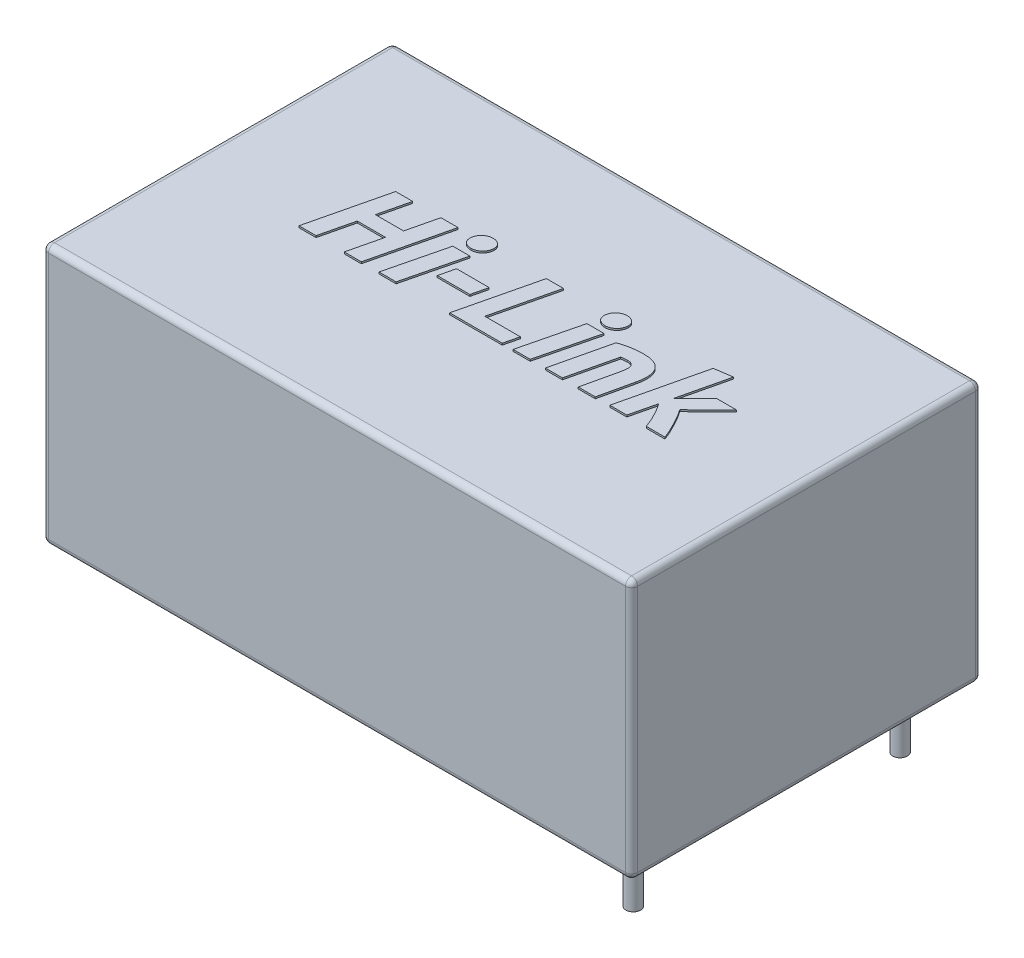
SolidWorks part; units mm, degrees
ref_plane "Front Plane" through (0, 0, 0) normal (0, 0, 1) x (1, 0, 0)
ref_plane "Top Plane" through (0, 0, 0) normal (0, 1, 0) x (1, 0, 0)
ref_plane "Right Plane" through (0, 0, 0) normal (1, 0, 0) x (0, 0, -1)
sketch "Sketch1" plane through (0, 0, 0) normal (0, 1, 0) x (1, 0, 0)
  line L1 (0, 0) -> (34, 0)
  line L2 (0, 0) -> (0, 20.2)
  line L3 (0, 20.2) -> (34, 20.2)
  line L4 (34, 0) -> (34, 20.2)
  dimension "D1" = 20.2
  dimension "D2" = 34
extrude "Boss-Extrude2" add sketch "Sketch1" along normal blind 15
sketch "Sketch2" plane through (0, 0, 0) normal (0, -1, 0) x (1, 0, 0)
  line L0 (0, -20.2) -> (0, 0) construction
  line L1 (0, 0) -> (34, 0) construction
  line L2 (34, 0) -> (34, -20.2) construction
  circle A0 centre (2.3, -7.6) radius 0.4233
  circle A1 centre (2.3, -12.6) radius 0.4233
  circle A2 centre (31.7, -17.8) radius 0.4233
  circle A3 centre (31.7, -2.4) radius 0.4233
  dimension "D3" = 0.8467
  dimension "D4" = 0.8467
  dimension "D7" = 0.8467
  dimension "D8" = 0.8467
  dimension "D1" = 2.3
  dimension "D2" = 7.6
  dimension "D5" = 5
  dimension "D6" = 15.4
  dimension "D9" = 2.3
  dimension "D10" = 2.4
extrude "Boss-Extrude3" add sketch "Sketch2" along normal blind 3.5
sketch "Sketch3" plane through (0, 15, 0) normal (0, 1, 0) x (1, 0, 0)
  text T0 "Hi-Link" font "Ubuntu" height 4.5
extrude "Boss-Extrude4" add sketch "Sketch3" along normal blind 0.1
fillet "Fillet1" radius 0.35 12 edges at (34, 7.5, -20.2) (34, 0, -10.1) (17, 0, -20.2) (0, 0, -10.1) (0, 7.5, -20.2) (17, 0, 0) (17, 15, -20.2) (34, 7.5, 0) (34, 15, -10.1) (0, 15, -10.1) (0, 7.5, 0) (17, 15, 0)
